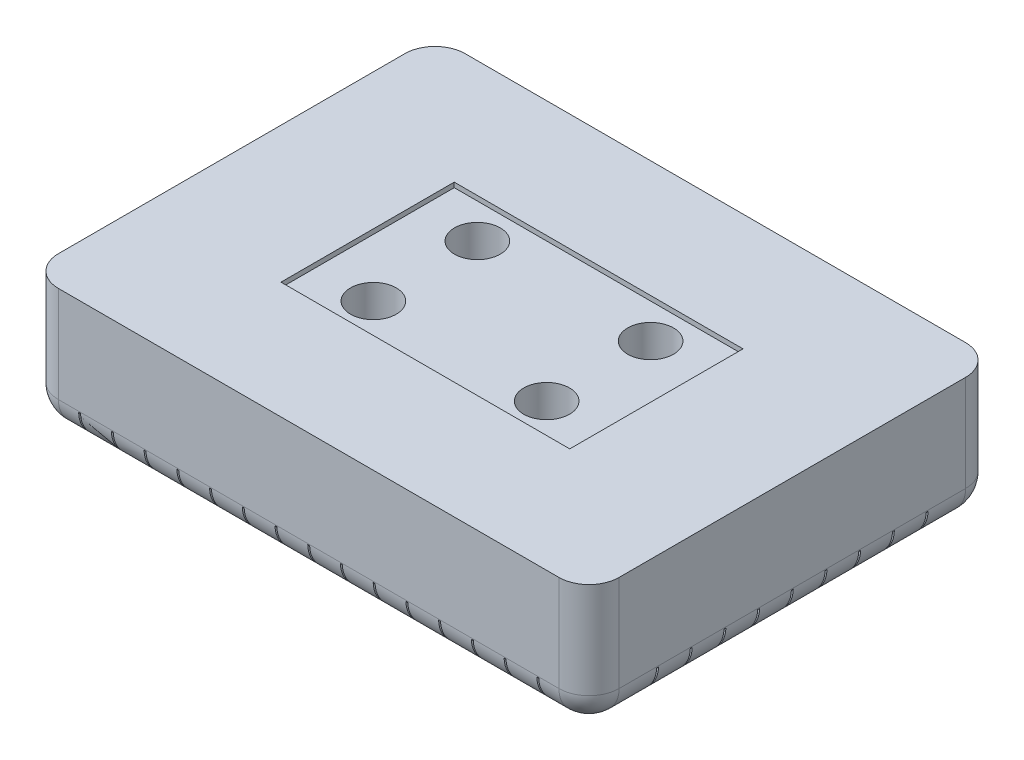
SolidWorks part; units mm, degrees
ref_plane "Front Plane" through (0, 0, 0) normal (0, 0, 1) x (1, 0, 0)
ref_plane "Top Plane" through (0, 0, 0) normal (0, 1, 0) x (1, 0, 0)
ref_plane "Right Plane" through (0, 0, 0) normal (1, 0, 0) x (0, 0, -1)
sketch "Sketch1" plane through (0, 0, 0) normal (0, 1, 0) x (1, 0, 0)
  line L0 (-4587.7595, 0) -> (224800.2139, 0) construction
  line L1 (0, -4587.7595) -> (0, 224800.2139) construction
  line L3 (369.8875, -268.2875) -> (-369.8875, -268.2875)
  line L4 (369.8875, -268.2875) -> (369.8875, 268.2875)
  line L5 (369.8875, 268.2875) -> (-369.8875, 268.2875)
  line L6 (-369.8875, -268.2875) -> (-369.8875, 268.2875)
  line L7 (369.8875, -268.2875) -> (-369.8875, 268.2875) construction
  line L8 (369.8875, 268.2875) -> (-369.8875, -268.2875) construction
  point P4 (0, 0)
  dimension "D1" = 536.575
  dimension "D2" = 739.775
extrude "Boss-Extrude1" add sketch "Sketch1" along normal blind 166.6875
fillet "Fillet1" radius 39.7002 8 edges at (-369.8875, 0, 0) (0, 0, -268.2875) (369.8875, 0, 0) (0, 0, 268.2875) (-369.8875, 83.3438, -268.2875) (369.8875, 83.3438, -268.2875) (369.8875, 83.3438, 268.2875) (-369.8875, 83.3438, 268.2875)
sketch "Sketch2" plane through (0, 0, 0) normal (1, 0, 0) x (0, 0, -1)
  line L0 (-1000, 0) -> (49000, 0) construction
  line L1 (0, -1000) -> (0, 49000) construction
  line L5 (228.6, -11.1125) -> (279.4, 52.3875)
  line L10 (279.4, 39.6875) -> (279.4, 52.3875)
  arc A0 (228.6, -11.1125) -> (279.4, 39.6875) centre (228.6, 39.6875) ccw
  arc A1 (228.6, -11.1125) -> (279.4, 39.6875) centre (228.6, 39.6875) ccw
  point P17 (279.4, -11.1125)
  dimension "D3" = 50.8
  dimension "D4" = 63.5
extrude "Cut-Extrude1" cut sketch "Sketch2" against normal mid plane 2.54
pattern_linear "LPattern1" count 8 spacing 43.18 along (1, 0, 0) count 8 spacing 43.18 along (-1, 0, 0) of "Cut-Extrude1"
mirror "Mirror1" about plane through (0, 0, 0) normal (0, 0, 1) of "Cut-Extrude1", "LPattern1"
sketch "Sketch3" plane through (0, 0, 0) normal (0, 0, 1) x (1, 0, 0)
  line L0 (-1000, 0) -> (49000, 0) construction
  line L1 (0, -1000) -> (0, 49000) construction
  line L2 (-381, 166.6875) -> (-381, 52.3875) construction
  line L3 (330.1873, 166.6875) -> (-330.1873, 166.6875) construction
  line L5 (-330.2, -11.1125) -> (-381, 52.3875)
  line L7 (0, 166.6875) -> (0, -11.1125)
  line L8 (0, -11.1125) -> (-330.2, -11.1125) construction
  line L9 (-381, 52.3875) -> (-381, 39.6875)
  line L10 (-381, 39.6875) -> (-381, 52.3875)
  arc A0 (-330.2, -11.1125) -> (-381, 39.6875) centre (-330.2, 39.6875) cw
  arc A1 (-330.2, -11.1125) -> (-381, 39.6875) centre (-330.2, 39.6875) cw
  point P17 (-381, -11.1125)
  dimension "D3" = 50.8
  dimension "D1" = 381
  dimension "D2" = 177.8
  dimension "D4" = 63.5
extrude "Cut-Extrude2" cut sketch "Sketch3" against normal mid plane 2.54 contours A0 L5 L9
pattern_linear "LPattern2" count 5 spacing 44.45 along (0, 0, -1) count 5 spacing 44.45 along (0, 0, 1) of "Cut-Extrude2"
mirror "Mirror2" about plane through (0, 0, 0) normal (1, 0, 0) of "Cut-Extrude2", "LPattern2"
sketch "Sketch4" plane through (0, 166.6875, 0) normal (0, 1, 0) x (1, 0, 0)
  line L0 (-1000, 0) -> (49000, 0) construction
  line L1 (0, -1000) -> (0, 49000) construction
  line L2 (-190.5, 0) -> (-190.5, 114.3) construction
  line L3 (0, -114.3) -> (-190.5, -114.3) construction
  line L4 (190.5, -114.3) -> (190.5, 0) construction
  line L5 (190.5, 114.3) -> (0, 114.3) construction
  line L6 (-190.5, -114.3) -> (-190.5, 0) construction
  line L7 (0, 114.3) -> (-190.5, 114.3) construction
  line L8 (190.5, 0) -> (190.5, 114.3) construction
  line L9 (190.5, -114.3) -> (0, -114.3) construction
  circle A0 centre (-114.3, 68.58) radius 30.1625
  circle A1 centre (-114.3, -68.58) radius 30.1625
  circle A2 centre (114.3, 68.58) radius 30.1625
  circle A3 centre (114.3, -68.58) radius 30.1625
  point P4 (0, 0)
  point P14 (-114.3, 68.58)
  dimension "D5" = 60.325
  dimension "D1" = 228.6
  dimension "D2" = 381
  dimension "D3" = 114.3
  dimension "D4" = 68.58
extrude "Cut-Extrude3" cut sketch "Sketch4" against normal through all
sketch "Sketch5" plane through (0, 166.6875, 0) normal (0, 1, 0) x (1, 0, 0)
  line L0 (-1000, 0) -> (49000, 0) construction
  line L1 (0, -1000) -> (0, 49000) construction
  line L3 (190.5, -114.3) -> (-190.5, -114.3)
  line L4 (190.5, -114.3) -> (190.5, 114.3)
  line L5 (190.5, 114.3) -> (-190.5, 114.3)
  line L6 (-190.5, -114.3) -> (-190.5, 114.3)
  line L7 (190.5, -114.3) -> (-190.5, 114.3) construction
  line L8 (190.5, 114.3) -> (-190.5, -114.3) construction
  point P4 (0, 0)
  dimension "D1" = 381
  dimension "D2" = 228.6
extrude "Cut-Extrude4" cut sketch "Sketch5" against normal blind 6.35
